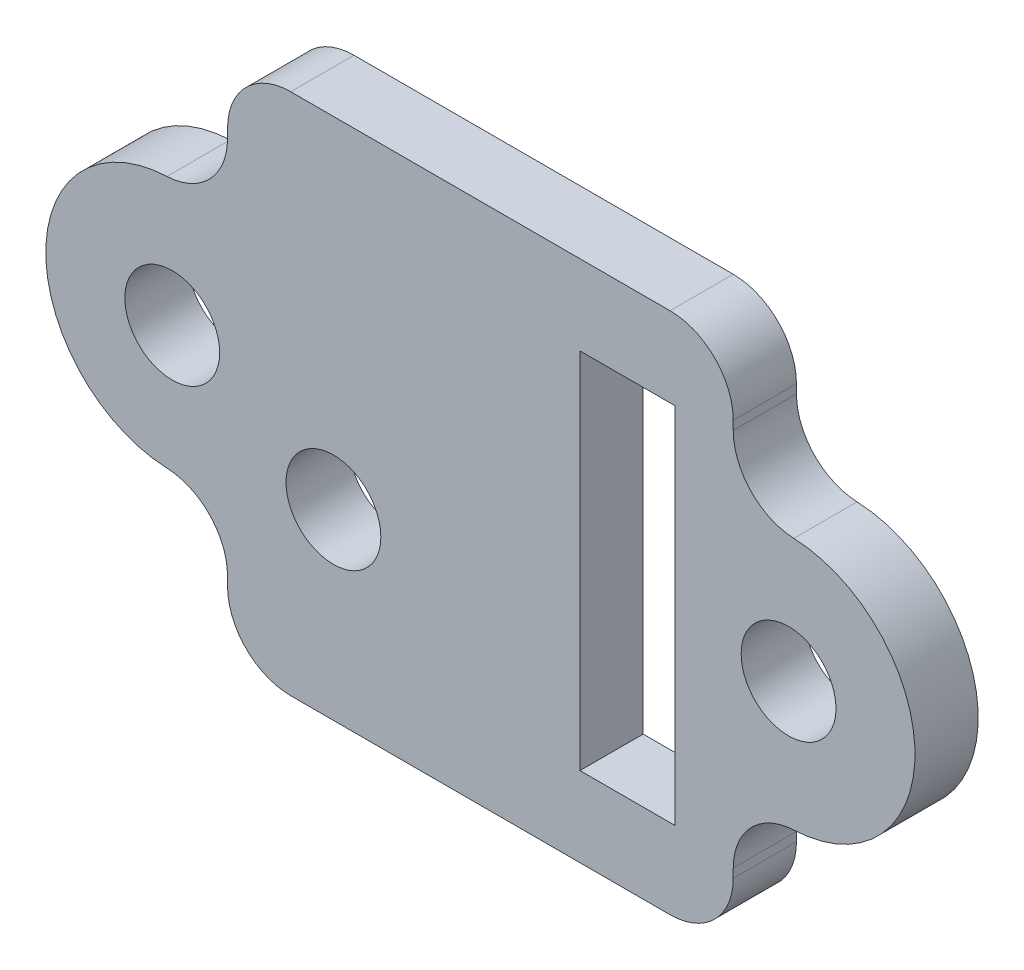
SolidWorks part; units mm, degrees
material "Acrylic (Medium-high impact)"
ref_plane "Plano frontal" through (0, 0, 0) normal (0, 0, 1) x (1, 0, 0)
ref_plane "Plano superior" through (0, 0, 0) normal (0, 1, 0) x (1, 0, 0)
ref_plane "Plano direito" through (0, 0, 0) normal (1, 0, 0) x (0, 0, -1)
sketch "Sketch1" plane through (0, 0, 0) normal (0, 0, 1) x (1, 0, 0)
  line L1 (8, -8.275) -> (-8, -8.275)
  line L2 (8, -8.275) -> (8, 8.275)
  line L3 (8, 8.275) -> (-8, 8.275)
  line L4 (-8, -8.275) -> (-8, 8.275)
  line L5 (8, -8.275) -> (-8, 8.275) construction
  line L6 (8, 8.275) -> (-8, -8.275) construction
  point P0 (0, 0)
  dimension "D1" = 16
  dimension "D2" = 16.55
extrude "Boss-Extrude1" add sketch "Sketch1" along normal mid plane 2
sketch "Sketch2" plane through (0, 0, 0) normal (0, 0, 1) x (1, 0, 0)
  line L0 (0, -1.1) -> (0, 1.1) construction
  line L1 (-9.75, 4) -> (-9.75, -4) construction
  line L2 (-9.75, 4) -> (-8, 4)
  line L3 (-8, 8.275) -> (-8, -8.275) construction
  line L4 (-9.75, -4) -> (-8, -4)
  line L5 (9.75, -4) -> (8, -4)
  line L6 (9.75, 4) -> (8, 4)
  line L7 (-8, 4) -> (-8, -4)
  line L8 (8, 4) -> (8, -4)
  circle A0 centre (-9.75, 0) radius 1.5
  circle A1 centre (9.75, 0) radius 1.5
  arc A2 (-9.75, 4) -> (-9.75, -4) centre (-9.75, 0) ccw
  arc A3 (9.75, 4) -> (9.75, -4) centre (9.75, 0) cw
  dimension "D1" = 3
  dimension "D3" = 2.5
  dimension "D4" = 19.5
extrude "Boss-Extrude2" add sketch "Sketch2" along normal mid plane 2
sketch "Sketch3" plane through (0, 0, 0) normal (0, 0, 1) x (1, 0, 0)
  line L0 (-6.15, -2.5) -> (6.15, -2.5) construction
  line L5 (3.15, 5.75) -> (6.15, 5.75)
  line L6 (8, 8.275) -> (-8, 8.275) construction
  line L7 (3.15, 5.75) -> (3.15, -5.75)
  line L8 (3.15, -5.75) -> (6.15, -5.75)
  line L9 (6.15, 5.75) -> (6.15, -5.75)
  line L11 (8, 4) -> (8, 8.275) construction
  circle A1 centre (-4.65, -2.5) radius 1.5
  point P6 (4.65, 5.75)
  point P8 (3.15, 0)
  point P11 (0, -2.5)
  dimension "D4" = 9.3
  dimension "D5" = 3
  dimension "D1" = 2.5
  dimension "D2" = 3
  dimension "D3" = 11.5
  dimension "D6" = 2.525
  dimension "D7" = 1.85
extrude "Cut-Extrude1" cut sketch "Sketch3" against normal through all both and the other way through all
fillet "Fillet1" radius 2 8 edges at (-8, -8.275, 0) (-8, -4, 0) (8, -8.275, 0) (8, -4, 0) (8, 4, 0) (8, 8.275, 0) (-8, 8.275, 0) (-8, 4, 0)
